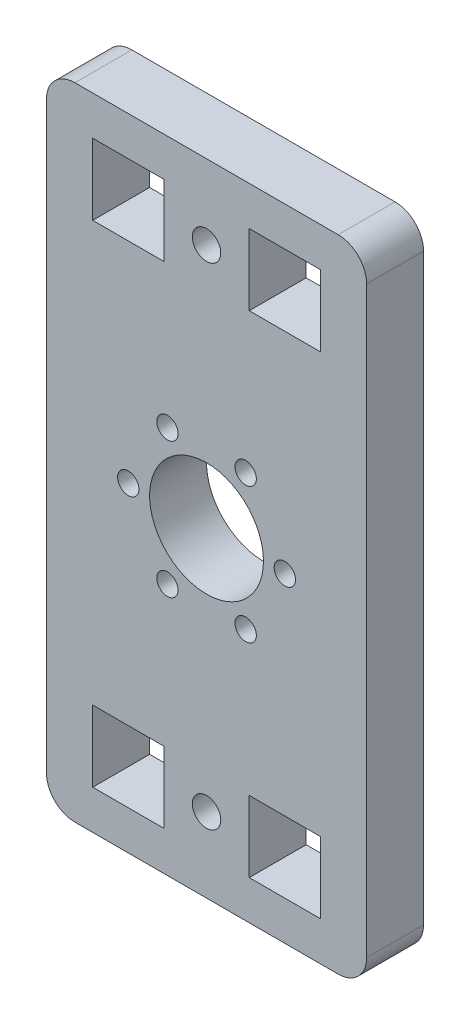
SolidWorks part; units mm, degrees
ref_plane "Front Plane" through (0, 0, 0) normal (0, 0, 1) x (1, 0, 0)
ref_plane "Top Plane" through (0, 0, 0) normal (0, 1, 0) x (1, 0, 0)
ref_plane "Right Plane" through (0, 0, 0) normal (1, 0, 0) x (0, 0, -1)
sketch "Sketch1" plane through (0, 0, 0) normal (0, 0, 1) x (1, 0, 0)
  line L0 (0, 0) -> (-11, 0) construction
  line L1 (18.5, -45) -> (-18.5, -45)
  line L2 (22.5, -41) -> (22.5, 41)
  line L3 (18.5, 45) -> (-18.5, 45)
  line L4 (-22.5, -41) -> (-22.5, 41)
  line L5 (22.5, -45) -> (-22.5, 45) construction
  line L6 (22.5, 45) -> (-22.5, -45) construction
  line L15 (0, 0) -> (0, -8.1671) construction
  line L16 (-16, -29.5) -> (-6, -29.5)
  line L17 (-16, -29.5) -> (-16, -39.5)
  line L18 (-16, -39.5) -> (-6, -39.5)
  line L19 (-6, -29.5) -> (-6, -39.5)
  line L20 (16, -39.5) -> (6, -39.5)
  line L21 (6, -29.5) -> (6, -39.5)
  line L22 (16, -29.5) -> (6, -29.5)
  line L23 (16, -29.5) -> (16, -39.5)
  line L24 (16, 29.5) -> (16, 39.5)
  line L25 (16, 29.5) -> (6, 29.5)
  line L26 (6, 29.5) -> (6, 39.5)
  line L27 (16, 39.5) -> (6, 39.5)
  line L28 (-16, 39.5) -> (-6, 39.5)
  line L29 (-6, 29.5) -> (-6, 39.5)
  line L30 (-16, 29.5) -> (-6, 29.5)
  line L31 (-16, 29.5) -> (-16, 39.5)
  circle A9 centre (0, 0) radius 8
  circle A10 centre (-11, 0) radius 1.5
  circle A11 centre (-5.5, 9.5263) radius 1.5
  circle A12 centre (5.5, 9.5263) radius 1.5
  circle A13 centre (11, 0) radius 1.5
  circle A14 centre (5.5, -9.5263) radius 1.5
  circle A15 centre (-5.5, -9.5263) radius 1.5
  circle A16 centre (0, -34.5) radius 2
  circle A17 centre (0, 34.5) radius 2
  arc A18 (18.5, -45) -> (22.5, -41) centre (18.5, -41) ccw
  arc A19 (-22.5, -41) -> (-18.5, -45) centre (-18.5, -41) ccw
  arc A20 (-22.5, 41) -> (-18.5, 45) centre (-18.5, 41) cw
  arc A21 (22.5, 41) -> (18.5, 45) centre (18.5, 41) ccw
  point P0 (0, 0)
  dimension "D5" = 6
  dimension "D8" = 4
  dimension "D9" = 0
  dimension "D11" = 5
  dimension "D16" = 16
  dimension "D19" = 3
  dimension "D10" = 4
  dimension "D2" = 45
  dimension "D3" = 10
  dimension "D4" = 45
  dimension "D6" = 10
  dimension "D7" = 29.5
  dimension "D17" = 11
  dimension "D18" = 0
  dimension "D21" = 11
  dimension "D22" = 11
  dimension "D20" = 6
extrude "Boss-Extrude2" add sketch "Sketch1" along normal blind 8
